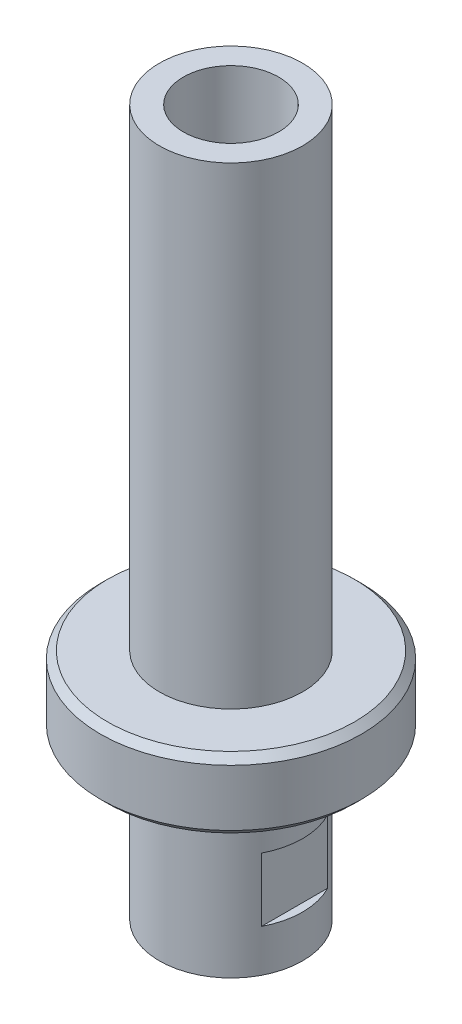
SolidWorks part; units mm, degrees
material "AISI 304"
ref_plane "Front Plane" through (0, 0, 0) normal (0, 0, 1) x (1, 0, 0)
ref_plane "Top Plane" through (0, 0, 0) normal (0, 1, 0) x (1, 0, 0)
ref_plane "Right Plane" through (0, 0, 0) normal (1, 0, 0) x (0, 0, -1)
sketch "Sketch1" plane through (0, 0, 0) normal (0, 0, 1) x (1, 0, 0)
  line L0 (0, -728.0045) -> (0, 35672.2211) construction
  line L1 (-728.0045, 0) -> (35672.2211, 0) construction
  line L2 (0, 100) -> (10.15, 100) construction
  line L3 (10.15, 100) -> (10.15, 33)
  line L4 (10.15, 0) -> (0, 0) construction
  line L5 (0, 0) -> (0, 100) construction
  line L6 (10.15, 23) -> (18.5, 23)
  line L7 (18.5, 23) -> (18.5, 33)
  line L8 (18.5, 33) -> (10.15, 33)
  line L9 (10.15, 23) -> (10.15, 0)
  line L10 (6.75, 100) -> (6.75, 0)
  line L11 (6.75, 100) -> (10.15, 100)
  line L12 (6.75, 0) -> (10.15, 0)
  dimension "D1" = 20.3
  dimension "D2" = 100
  dimension "D3" = 10
  dimension "D4" = 37
  dimension "D5" = 23
  dimension "D6" = 13.5
revolve "Revolve1" add sketch "Sketch1" angle 360 about L0
sketch "Sketch2" plane through (0, 0, 0) normal (0, 0, 1) x (1, 0, 0)
  line L0 (0, -1000) -> (0, 49000) construction
  line L2 (9, 6) -> (12, 6)
  line L3 (9, 6) -> (9, 15)
  line L4 (9, 15) -> (12, 15)
  line L5 (12, 6) -> (12, 15)
  line L6 (9, 6) -> (12, 15) construction
  line L7 (9, 15) -> (12, 6) construction
  line L8 (-9, 15) -> (-12, 15)
  line L9 (-12, 6) -> (-12, 15)
  line L10 (-9, 6) -> (-12, 6)
  line L11 (-9, 6) -> (-9, 15)
  point P1 (10.5, 10.5)
  dimension "D1" = 18
  dimension "D2" = 6
  dimension "D3" = 3
  dimension "D4" = 9
extrude "Cut-Extrude1" cut sketch "Sketch2" against normal through all both and the other way through all
chamfer "Chamfer1" distance 1 angle 45 2 edges at (18.5, 23, 0) (18.5, 33, 0)
